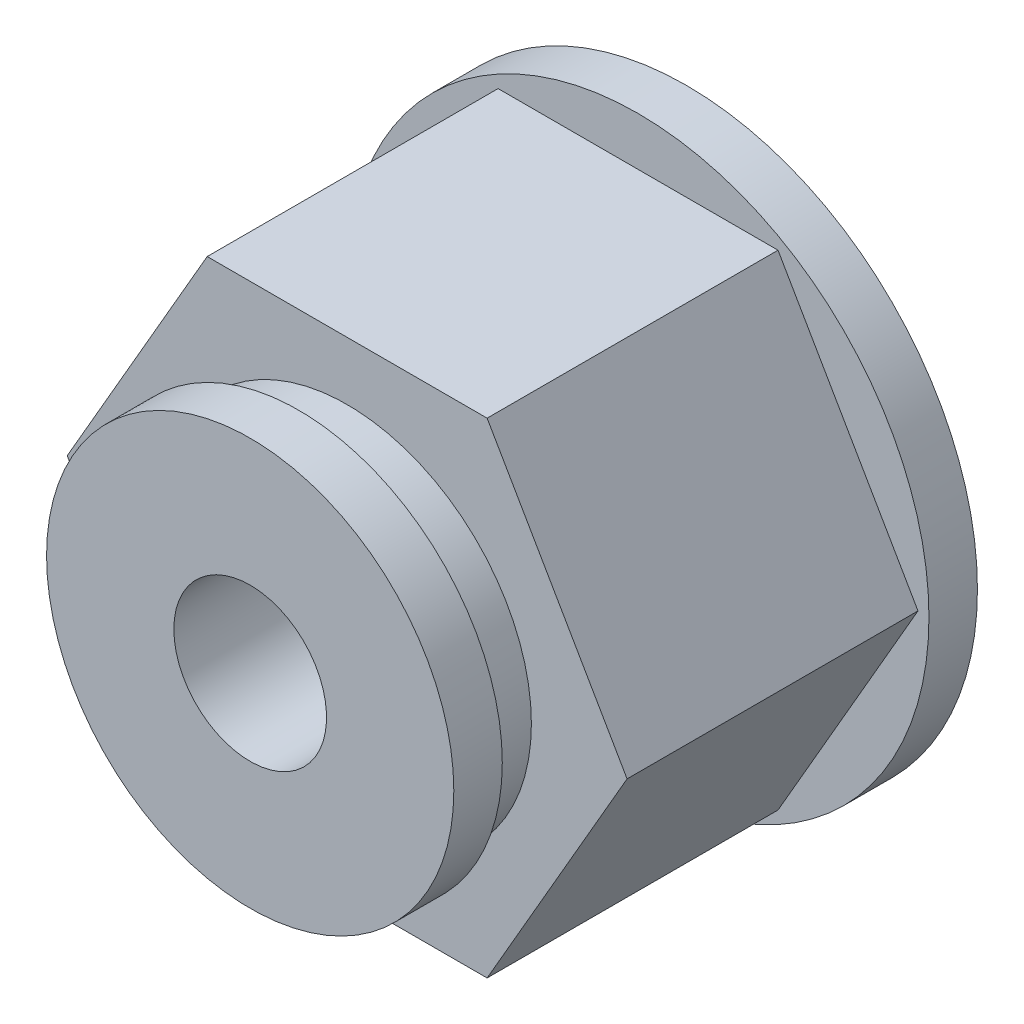
SolidWorks part; units mm, degrees
ref_plane "Plan de face" through (0, 0, 0) normal (0, 0, 1) x (1, 0, 0)
ref_plane "Plan de dessus" through (0, 0, 0) normal (0, 1, 0) x (1, 0, 0)
ref_plane "Plan de droite" through (0, 0, 0) normal (1, 0, 0) x (0, 0, -1)
sketch "Esquisse1" plane through (0, 0, 0) normal (0, 0, 1) x (1, 0, 0)
  line L1 (7.3323, 0) -> (3.6662, 6.35)
  line L2 (3.6662, 6.35) -> (-3.6662, 6.35)
  line L3 (-3.6662, 6.35) -> (-7.3323, 0)
  line L4 (-7.3323, 0) -> (-3.6662, -6.35)
  line L5 (-3.6662, -6.35) -> (3.6662, -6.35)
  line L6 (3.6662, -6.35) -> (7.3323, 0)
  circle A0 centre (0, 0) radius 6.35 construction
  dimension "D1" = 12.7
extrude "Boss.-Extru.1" add sketch "Esquisse1" along normal mid plane 7.62
sketch "Esquisse2" plane through (0, 0, -3.81) normal (0, 0, -1) x (-1, 0, 0)
  circle A0 centre (0, 0) radius 7.62
  dimension "D1" = 15.24
extrude "Boss.-Extru.2" add sketch "Esquisse2" along normal blind 1.27
sketch "Esquisse3" plane through (0, 0, 3.81) normal (0, 0, 1) x (1, 0, 0)
  circle A0 centre (0, 0) radius 4.826
  dimension "D1" = 9.652
extrude "Boss.-Extru.3" add sketch "Esquisse3" along normal blind 1.27
sketch "Esquisse4" plane through (0, 0, 5.08) normal (0, 0, 1) x (1, 0, 0)
  circle A0 centre (0, 0) radius 5.334
  dimension "D1" = 10.668
extrude "Boss.-Extru.4" add sketch "Esquisse4" along normal blind 1.27
sketch "Esquisse5" plane through (0, 0, -5.08) normal (0, 0, -1) x (-1, 0, 0)
  circle A0 centre (0, 0) radius 2
  dimension "D1" = 4
extrude "Enlèv. mat.-Extru.1" cut sketch "Esquisse5" against normal through all
